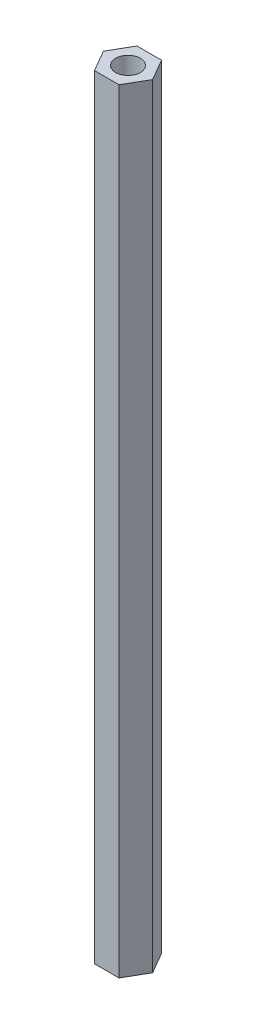
SolidWorks part; units mm, degrees
material "尼龙 6/10"
ref_plane "前视基准面" through (0, 0, 0) normal (0, 0, 1) x (1, 0, 0)
ref_plane "上视基准面" through (0, 0, 0) normal (0, 1, 0) x (1, 0, 0)
ref_plane "右视基准面" through (0, 0, 0) normal (1, 0, 0) x (0, 0, -1)
sketch "草图1" plane through (0, 0, 0) normal (0, 1, 0) x (1, 0, 0)
  line L1 (3.1754, 0) -> (1.5877, 2.75)
  line L2 (1.5877, 2.75) -> (-1.5877, 2.75)
  line L3 (-1.5877, 2.75) -> (-3.1754, 0)
  line L4 (-3.1754, 0) -> (-1.5877, -2.75)
  line L5 (-1.5877, -2.75) -> (1.5877, -2.75)
  line L6 (1.5877, -2.75) -> (3.1754, 0)
  circle A0 centre (0, 0) radius 2.75 construction
  dimension "D1" = 5.5
extrude "凸台-拉伸1" add sketch "草图1" along normal blind 100
sketch "草图2" plane through (0, 100, 0) normal (0, 1, 0) x (1, 0, 0)
  circle A0 centre (0, 0) radius 1.6
  dimension "D1" = 3.2
extrude "切除-拉伸1" cut sketch "草图2" against normal through all
